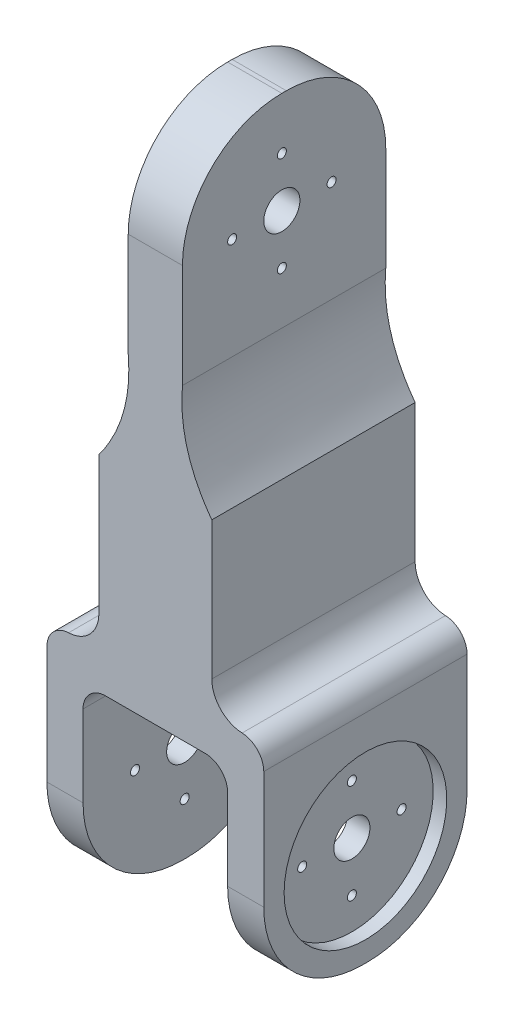
SolidWorks part; units mm, degrees
ref_plane "Front Plane" through (0, 0, 0) normal (0, 0, 1) x (1, 0, 0)
ref_plane "Top Plane" through (0, 0, 0) normal (0, 1, 0) x (1, 0, 0)
ref_plane "Right Plane" through (0, 0, 0) normal (1, 0, 0) x (0, 0, -1)
sketch "Sketch2" plane through (0, 0, 0) normal (0, 1, 0) x (1, 0, 0)
  line L1 (24, -22.5) -> (-24, -22.5)
  line L2 (24, -22.5) -> (24, 22.5)
  line L3 (24, 22.5) -> (-24, 22.5)
  line L4 (-24, -22.5) -> (-24, 22.5)
  line L5 (24, -22.5) -> (-24, 22.5) construction
  line L6 (24, 22.5) -> (-24, -22.5) construction
  point P0 (0, 0)
  dimension "D1" = 48
  dimension "D2" = 45
extrude "Boss-Extrude1" add sketch "Sketch2" along normal blind 8
sketch "Sketch3" plane through (24, 0, 0) normal (1, 0, 0) x (0, 0, -1)
  line L0 (-22.5, 0) -> (22.5, -45) construction
  line L1 (-22.5, 0) -> (22.5, 0)
  line L2 (-22.5, 0) -> (-22.5, -23)
  line L3 (-0.5, -45) -> (0.5, -45)
  line L4 (22.5, 0) -> (22.5, -23)
  line L5 (22.5, 0) -> (0, -22.5) construction
  arc A1 (0.5, -45) -> (22.5, -23) centre (0.5, -23) ccw
  arc A2 (-22.5, -23) -> (-0.5, -45) centre (-0.5, -23) ccw
  dimension "D2" = 22
  dimension "D1" = 45
extrude "Boss-Extrude2" add sketch "Sketch3" against normal blind 8
sketch "Sketch4" plane through (16, 0, 0) normal (-1, 0, 0) x (0, 0, 1)
  line L0 (-22.5, 0) -> (22.5, 0) construction
  line L3 (-22.5, -23) -> (-22.5, 0) construction
  circle A0 centre (0, -22.5) radius 18
  dimension "D1" = 22.5
  dimension "D3" = 36
  dimension "D2" = 22.5
extrude "Cut-Extrude1" cut sketch "Sketch4" along normal blind 3 from surface at -8 starting at face at (24, -21.5188, 0)
sketch "Sketch5" plane through (21, 0, 0) normal (1, 0, 0) x (0, 0, -1)
  line L0 (0, -4.5) -> (0, -40.5) construction
  line L1 (18, -22.5) -> (-18, -22.5) construction
  circle A0 centre (0, -22.5) radius 4
  circle A1 centre (0, -22.5) radius 18 construction
  circle A2 centre (0, -22.5) radius 18 construction
  circle A3 centre (0, -11.5) radius 1
  circle A4 centre (11, -22.5) radius 1
  circle A5 centre (0, -33.5) radius 1
  circle A6 centre (-11, -22.5) radius 1
  dimension "D1" = 8
  dimension "D3" = 2
  dimension "D4" = 11
  dimension "D2" = 11
  dimension "D5" = 11
  dimension "D6" = 11
extrude "Cut-Extrude2" cut sketch "Sketch5" against normal through all
mirror "Mirror1" about plane through (0, 0, 0) normal (1, 0, 0) of bodies 104
sketch "Sketch6" plane through (0, 8, 0) normal (0, 1, 0) x (1, 0, 0)
  line L0 (-24, -22.5) -> (24, -22.5) construction
  line L1 (-12.5, 22.5) -> (12.5, 22.5)
  line L2 (-12.5, 22.5) -> (-12.5, -22.5)
  line L3 (-12.5, -22.5) -> (12.5, -22.5)
  line L4 (12.5, 22.5) -> (12.5, -22.5)
  line L5 (-12.5, 22.5) -> (12.5, -22.5) construction
  line L6 (-12.5, -22.5) -> (12.5, 22.5) construction
  point P0 (0, 0)
  dimension "D1" = 25
extrude "Boss-Extrude3" add sketch "Sketch6" along normal blind 60
fillet "Fillet7" radius 5 2 edges at (16, 0, 0) (-16, 0, 0)
sketch "Sketch7" plane through (0, 68, 0) normal (0, 1, 0) x (1, 0, 0)
  line L0 (-12.5, -22.5) -> (12.5, -22.5) construction
  line L1 (-6, 22.5) -> (6, 22.5)
  line L2 (-6, 22.5) -> (-6, -22.5)
  line L3 (-6, -22.5) -> (6, -22.5)
  line L4 (6, 22.5) -> (6, -22.5)
  line L5 (-6, 22.5) -> (6, -22.5) construction
  line L6 (-6, -22.5) -> (6, 22.5) construction
  point P0 (0, 0)
  dimension "D1" = 12
extrude "Boss-Extrude4" add sketch "Sketch7" along normal blind 45
fillet "Fillet10" radius 22 2 edges at (0, 113, -22.5) (0, 113, 22.5)
sketch "Sketch8" plane through (-6, 0, 0) normal (-1, 0, 0) x (0, 0, 1)
  line L0 (0.5, 113) -> (0.5, 90.5)
  circle A0 centre (0.5, 90.5) radius 18
  dimension "D2" = 36
  dimension "D1" = 22.5
extrude "Cut-Extrude3" cut sketch "Sketch8" against normal blind 3
sketch "Sketch9" plane through (-3, 0, 0) normal (-1, 0, 0) x (0, 0, 1)
  line L0 (0.5, 108.5) -> (0.5, 72.5) construction
  line L1 (-17.5, 90.5) -> (18.5, 90.5) construction
  circle A0 centre (0.5, 90.5) radius 4
  circle A1 centre (0.5, 90.5) radius 18 construction
  circle A2 centre (0.5, 90.5) radius 18 construction
  circle A3 centre (0.5, 101.5) radius 1
  circle A4 centre (11.5, 90.5) radius 1
  circle A5 centre (0.5, 79.5) radius 1
  circle A6 centre (-10.5, 90.5) radius 1
  dimension "D1" = 8
  dimension "D3" = 2
  dimension "D5" = 2
  dimension "D2" = 11
  dimension "D4" = 11
extrude "Cut-Extrude4" cut sketch "Sketch9" against normal through all
sketch "Sketch10" plane through (0, 0, -22.5) normal (0, 0, -1) x (-1, 0, 0)
  line L0 (12.5, 68) -> (12.5, 8) construction
  line L1 (6, 68) -> (12.5, 68)
  line L2 (12.5, 68) -> (12.5, 45.4931)
  line L3 (0, 113) -> (0, 45.4931)
  line L4 (-6, 113) -> (6, 113) construction
  line L5 (-12.5, 68) -> (-12.5, 45.4931)
  line L6 (-6, 68) -> (-12.5, 68)
  spline S0 degree 2 poles (6, 68) (4.9386, 55.683) (12.5, 45.4931) knots 0 0 0 1 1 1
  spline S1 degree 2 poles (-6, 68) (-4.9386, 55.683) (-12.5, 45.4931) knots 0 0 0 1 1 1
  line M7 (-6, 68) -> (-12.5, 68)
  line M8 (-12.5, 68) -> (-12.5, 8)
  line M20 (12.5, 8) -> (12.5, 68)
  line M21 (12.5, 68) -> (6, 68)
extrude "Cut-Extrude5" cut sketch "Sketch10" against normal through all contours S0 M21 M20 | S1 M7 M8
fillet "Fillet11" radius 5 2 edges at (24, 8, 0) (-24, 8, 0)
fillet "Fillet12" radius 7 2 edges at (-12.5, 8, 0) (12.5, 8, 0)
